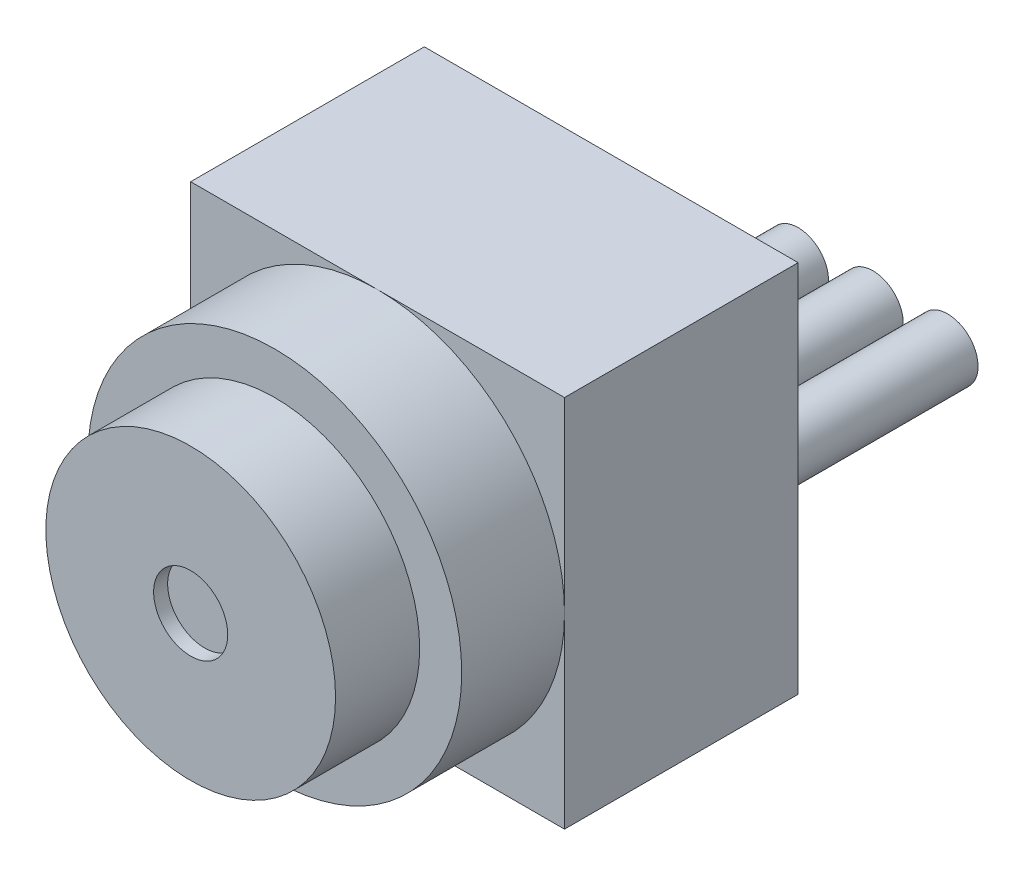
SolidWorks part; units mm, degrees
ref_plane "Front Plane" through (0, 0, 0) normal (0, 0, 1) x (1, 0, 0)
ref_plane "Top Plane" through (0, 0, 0) normal (0, 1, 0) x (1, 0, 0)
ref_plane "Right Plane" through (0, 0, 0) normal (1, 0, 0) x (0, 0, -1)
sketch "Sketch1" plane through (0, 0, 0) normal (0, 0, 1) x (1, 0, 0)
  line L1 (0, 0) -> (10.16, 0)
  line L2 (0, 0) -> (0, 10.16)
  line L3 (0, 10.16) -> (10.16, 10.16)
  line L4 (10.16, 0) -> (10.16, 10.16)
  dimension "D1" = 10.16
  dimension "D2" = 10.16
extrude "Extrude1" add sketch "Sketch1" along normal blind 6.35
sketch "Sketch2" plane through (0, 0, 6.35) normal (0, 0, 1) x (1, 0, 0)
  line L0 (0, 10.16) -> (10.16, 0) construction
  circle A0 centre (5.08, 5.08) radius 5.08
  dimension "D1" = 10.16
extrude "Extrude2" add sketch "Sketch2" along normal blind 2.794
sketch "Sketch3" plane through (0, 0, 9.144) normal (0, 0, 1) x (1, 0, 0)
  circle A0 centre (5.08, 5.08) radius 3.937
  dimension "D1" = 7.874
extrude "Extrude3" add sketch "Sketch3" along normal blind 2.286
sketch "Sketch4" plane through (0, 0, 11.43) normal (0, 0, 1) x (1, 0, 0)
  circle A0 centre (5.08, 5.08) radius 1.0071
extrude "Extrude4" cut sketch "Sketch4" against normal blind 0.381
sketch "Sketch5" plane through (0, 0, 0) normal (0, 0, -1) x (-1, 0, 0)
  line L0 (-10.16, 5.08) -> (-5.08, 5.08) construction
  line L1 (-10.16, 0) -> (-10.16, 10.16) construction
  circle A0 centre (-5.08, 5.08) radius 0.8255
  circle A1 centre (-7.112, 5.08) radius 0.8255
  circle A2 centre (-9.144, 5.08) radius 0.8255
  dimension "D1" = 1.651
  dimension "D2" = 1.651
  dimension "D3" = 1.651
  dimension "D4" = 2.032
  dimension "D5" = 2.032
extrude "Extrude5" add sketch "Sketch5" along normal blind 5.08
